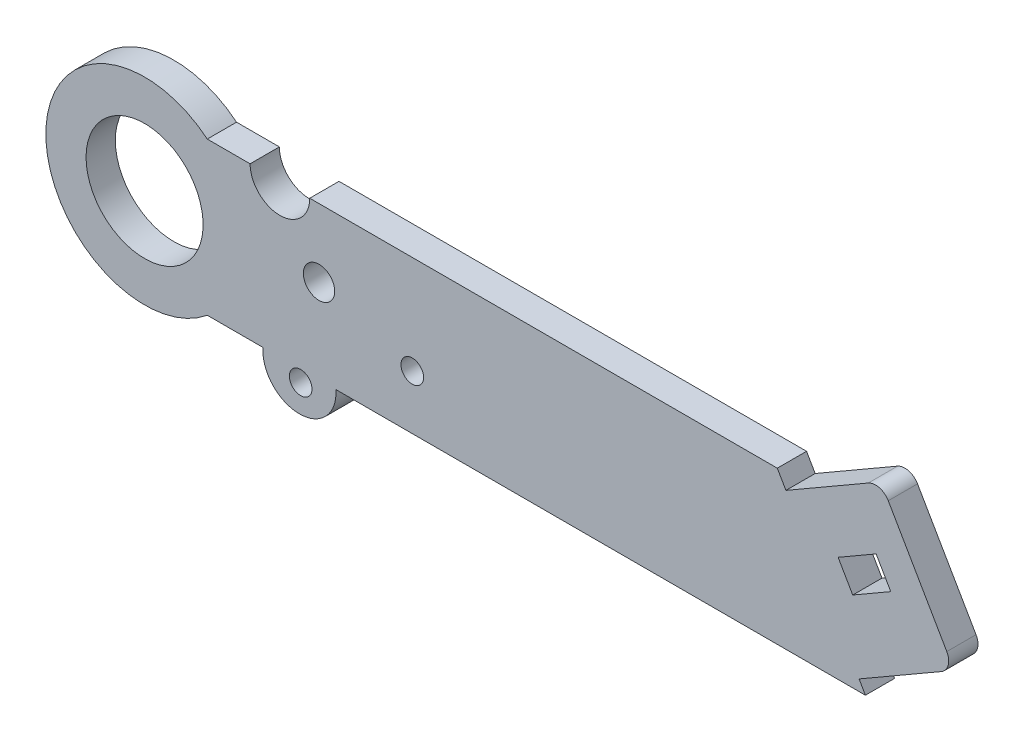
SolidWorks part; units mm, degrees
ref_plane "Ebene vorne" through (0, 0, 0) normal (0, 0, 1) x (1, 0, 0)
ref_plane "Ebene oben" through (0, 0, 0) normal (0, 1, 0) x (1, 0, 0)
ref_plane "Ebene rechts" through (0, 0, 0) normal (1, 0, 0) x (0, 0, -1)
sketch "Skizze1" plane through (0, 0, 0) normal (0, 0, 1) x (1, 0, 0)
  line L0 (28.5706, -10.4305) -> (-71.4294, -10.4305)
  line L7 (-71.4294, 10.4305) -> (-65.5753, 10.4305)
  line L8 (-57.4235, 10.4305) -> (28.5706, 10.4305)
  line L9 (-106.0055, 0) -> (28.1497, 0) construction
  arc A3 (-65.5753, 10.4305) -> (-57.4235, 10.4305) centre (-61.4994, 10.4305) ccw
  arc A6 (-71.4294, 10.4305) -> (-71.4294, -10.4305) centre (-80, 0) ccw
  arc A7 (28.5706, 10.4305) -> (28.5706, -10.4305) centre (28.5706, 0) cw
  dimension "D4" = 5.8542
  dimension "D2" = 20.861
  dimension "D1" = 13.5
  dimension "D3" = 4.0759
  dimension "D5" = 100
  dimension "D6" = 10.4305
extrude "Aufsatz-Linear austragen1" add sketch "Skizze1" along normal blind 4
sketch "Skizze2" plane through (0, 0, 4) normal (0, 0, 1) x (1, 0, 0)
  line L0 (14.8038, 4.0336) -> (20, 7.0336)
  line L5 (14.8038, 4.0336) -> (16.8038, 0.5695)
  line L6 (20, 7.0336) -> (22, 3.5695)
  line L7 (16.8038, 0.5695) -> (22, 3.5695)
  line L8 (-71.4294, -10.4305) -> (28.5706, -10.4305) construction
  line L9 (28.5706, 10.4305) -> (-57.4235, 10.4305) construction
  circle A1 centre (-80, 0) radius 8
  circle A2 centre (-56.1528, 1.1059) radius 2.1413
  dimension "D1" = 4
  dimension "D2" = 16
  dimension "D8" = 4.2826
  dimension "D3" = 6
  dimension "D4" = 14
  dimension "D5" = 80
  dimension "D6" = 56.1528
  dimension "D7" = 1.1059
  dimension "D9" = 22
  dimension "D10" = 60
extrude "Schnitt-Linear austragen1" cut sketch "Skizze2" against normal up to next
sketch "Skizze3" plane through (0, 0, 4) normal (0, 0, 1) x (1, 0, 0)
  line L0 (34.5264, 28.4006) -> (53.5933, -4.6243)
  line L1 (17.6699, -8.9305) -> (28.9282, -2.4305)
  line L2 (5.7191, 11.7688) -> (7.6699, 8.39)
  line L7 (17.6699, -8.9305) -> (24.7861, -21.2561)
  line L8 (5.7191, 11.7688) -> (34.5264, 28.4006)
  line L10 (53.5933, -4.6243) -> (24.7861, -21.2561)
  line L11 (14.8038, 4.0336) -> (16.8038, 0.5695) construction
  line L12 (28.9282, -2.4305) -> (18.9282, 14.89)
  line L13 (18.9282, 14.89) -> (7.6699, 8.39)
  line L14 (-71.4294, -10.4305) -> (28.5706, -10.4305) construction
  dimension "D1" = 20
  dimension "D2" = 1.5
  dimension "D3" = 4
  dimension "D4" = 13
extrude "Schnitt-Linear austragen2" cut sketch "Skizze3" against normal up to next
sketch "Skizze4" plane through (0, 0, 0) normal (0, 0, 1) x (1, 0, 0)
  line L0 (11.2042, 10.4305) -> (18.9282, 14.89)
  line L1 (21.6603, 14.1579) -> (29.6603, 0.3015)
  line L3 (11.2042, 10.4305) -> (21.5029, 10.4305)
  line L4 (21.5029, 10.4305) -> (28.9282, -2.4305)
  line L5 (17.6699, -8.9305) -> (18.5359, -10.4305) construction
  line L6 (12.6138, -9.5402) -> (34.8321, 3.2875) construction
  line L7 (28.9282, -2.4305) -> (17.6699, -8.9305) construction
  line L8 (2.9376, 3.3484) -> (32.3703, 20.3414) construction
  arc A0 (28.9282, -2.4305) -> (29.6603, 0.3015) centre (27.9282, -0.6985) ccw
  arc A1 (18.9282, 14.89) -> (21.6603, 14.1579) centre (19.9282, 13.1579) cw
  dimension "D2" = 2
  dimension "D3" = 2
  dimension "D1" = 15
extrude "Aufsatz-Linear austragen3" add sketch "Skizze4" along normal up to surface (4 mm away) up to face at (-54.0115, 1.1059, 4)
sketch "Skizze5" plane through (0, 0, 4) normal (0, 0, 1) x (1, 0, 0)
  line L0 (-71.4294, -10.4305) -> (18.5359, -10.4305) construction
  line L1 (-63.8151, -10.4305) -> (-53.8438, -10.4305)
  arc A0 (-63.8151, -10.4305) -> (-53.8438, -10.4305) centre (-58.8294, -10.8085) ccw
  dimension "D1" = 5
  dimension "D2" = 12.6
  dimension "D3" = 0.378
extrude "Aufsatz-Linear austragen4" add sketch "Skizze5" against normal up to surface (4 mm away) contours A0 L1 up to face at (-11.4722, 3.6315, 0)
sketch "Skizze6" plane through (0, 0, 4) normal (0, 0, 1) x (1, 0, 0)
  circle A0 centre (-58.6634, -12.0125) radius 1.55
  arc A1 (-63.8151, -10.4305) -> (-53.8438, -10.4305) centre (-58.8294, -10.8085) ccw construction
  circle A2 centre (-43.4044, -3.0255) radius 1.55
  dimension "D1" = 3.1
  dimension "D3" = 0.166
  dimension "D2" = 1.204
  dimension "D4" = 15.259
  dimension "D5" = 8.987
extrude "Schnitt-Linear austragen3" cut sketch "Skizze6" against normal up to next
